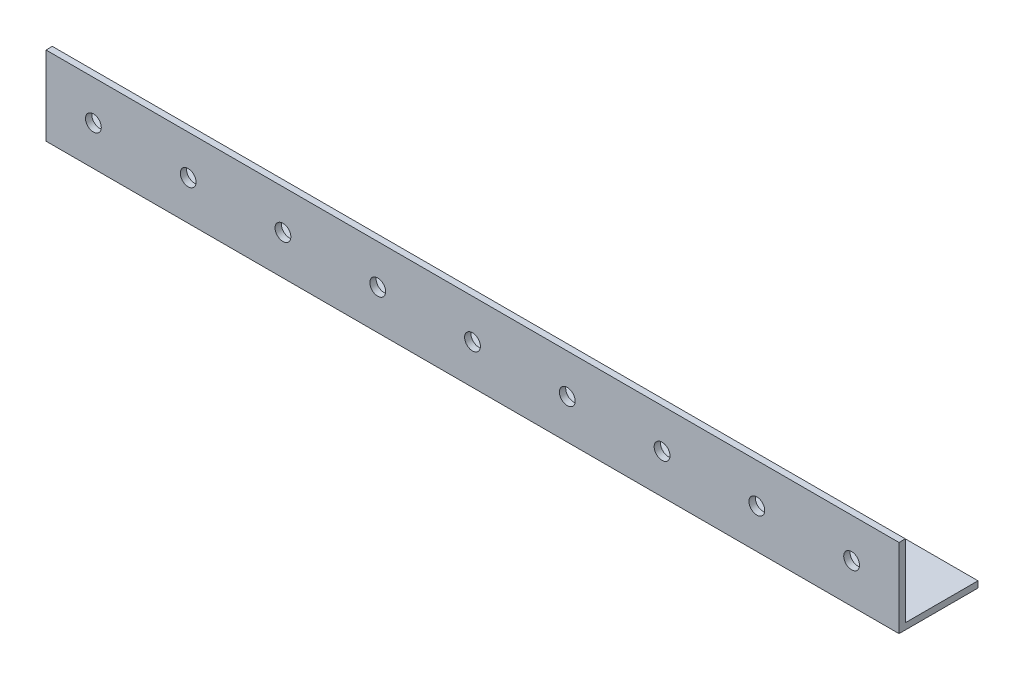
SolidWorks part; units mm, degrees
ref_plane "Спереди" through (0, 0, 0) normal (0, 0, 1) x (1, 0, 0)
ref_plane "Сверху" through (0, 0, 0) normal (0, 1, 0) x (1, 0, 0)
ref_plane "Справа" through (0, 0, 0) normal (1, 0, 0) x (0, 0, -1)
sketch "Эскиз1" plane through (0, 0, 0) normal (1, 0, 0) x (0, 0, -1)
  line L0 (0, 0) -> (0, 50)
  line L1 (0, 0) -> (50, 0)
  dimension "D1" = 50
  dimension "D2" = 50
extrude "Вытянуть-Тонкостенный1" add sketch "Эскиз1" along normal blind 540 thin
sketch "Эскиз2" plane through (0, 0, 0) normal (0, 0, 1) x (1, 0, 0)
  circle A0 centre (30, 25) radius 5
  circle A1 centre (90, 25) radius 5
  circle A2 centre (150, 25) radius 5
  circle A3 centre (210, 25) radius 5
  circle A8 centre (270, 25) radius 5
  circle A29 centre (330, 25) radius 5
  circle A30 centre (390, 25) radius 5
  circle A31 centre (450, 25) radius 5
  circle A32 centre (510, 25) radius 5
  dimension "D1" = 9
extrude "Вырез-Вытянуть1" cut sketch "Эскиз2" against normal through all
sketch "Эскиз3" plane through (0, 0, 0) normal (0, -1, 0) x (1, 0, 0)
  circle A0 centre (30, -25) radius 5
  circle A1 centre (90, -25) radius 5
  circle A2 centre (150, -25) radius 5
  circle A3 centre (210, -25) radius 5
  circle A4 centre (270, -25) radius 5
  circle A5 centre (330, -25) radius 5
  circle A6 centre (390, -25) radius 5
  circle A7 centre (450, -25) radius 5
  circle A8 centre (510, -25) radius 5
  dimension "D1" = 9
extrude "Вырез-Вытянуть2" cut sketch "Эскиз3" against normal through all
